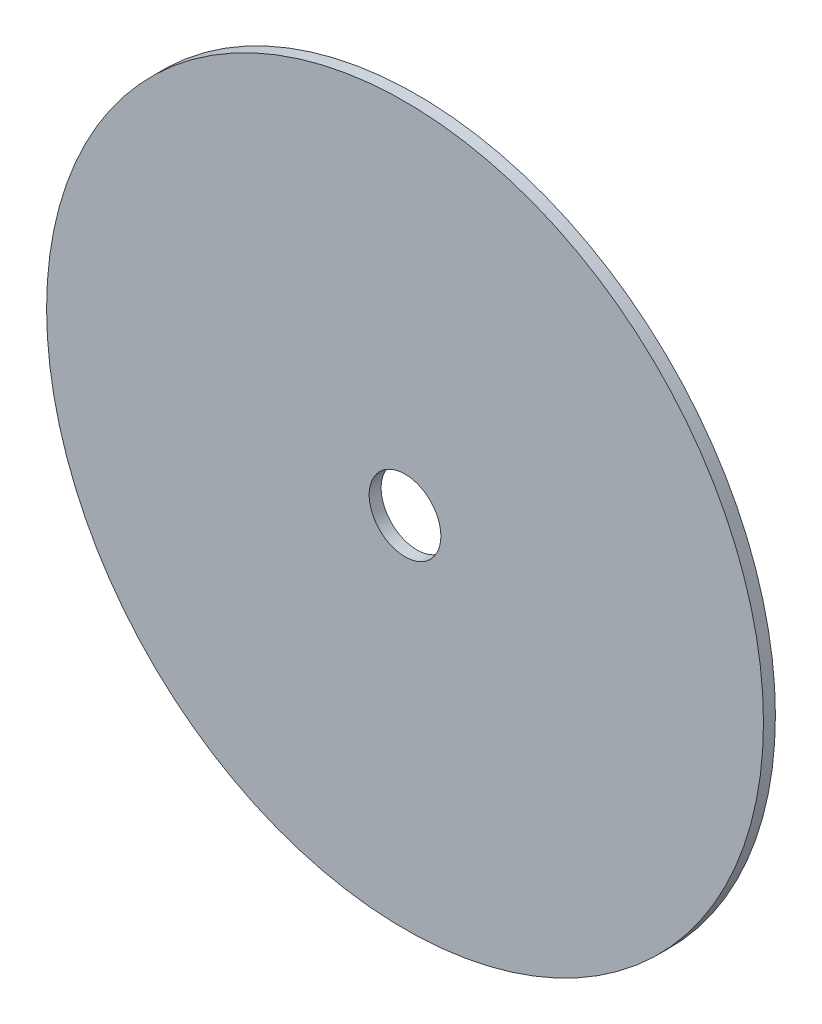
SolidWorks part; units mm, degrees
ref_plane "Płaszczyzna przednia" through (0, 0, 0) normal (0, 0, 1) x (1, 0, 0)
ref_plane "Płaszczyzna górna" through (0, 0, 0) normal (0, 1, 0) x (1, 0, 0)
ref_plane "Płaszczyzna prawa" through (0, 0, 0) normal (1, 0, 0) x (0, 0, -1)
sketch "Szkic1" plane through (0, 0, 0) normal (0, 0, 1) x (1, 0, 0)
  circle A0 centre (0, 0) radius 15
  circle A1 centre (0, 0) radius 1.1
  circle A2 centre (0, 0) radius 1.5
  dimension "D1" = 2.2
  dimension "D2" = 30
  dimension "D3" = 3
extrude "Dodanie-wyciągnięcie1" add sketch "Szkic1" along normal blind 0.5 contours A0 A2
